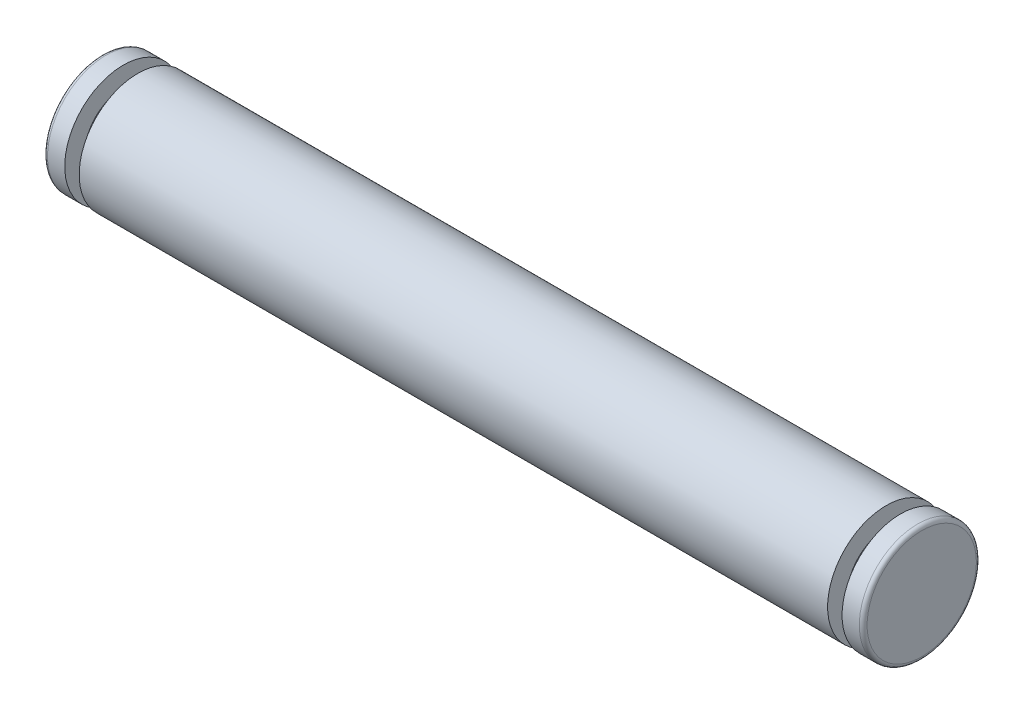
SolidWorks part; units mm, degrees
ref_plane "Front Plane" through (0, 0, 0) normal (0, 0, 1) x (1, 0, 0)
ref_plane "Top Plane" through (0, 0, 0) normal (0, 1, 0) x (1, 0, 0)
ref_plane "Right Plane" through (0, 0, 0) normal (1, 0, 0) x (0, 0, -1)
sketch "Sketch1" plane through (0, 0, 0) normal (0, 1, 0) x (1, 0, 0)
  line L0 (-21, 0) -> (0, 0) construction
  line L1 (0, 0) -> (21, 0) construction
  line L2 (0, 0) -> (0, 4.0847) construction
  line L3 (-19.177, 3) -> (19.177, 3)
  line L4 (19.177, 3) -> (19.177, 2)
  line L5 (19.177, 2) -> (19.917, 2)
  line L6 (19.917, 2) -> (19.917, 3)
  line L7 (19.917, 3) -> (20.8, 3)
  line L8 (21, 2.8) -> (21, 0)
  line L9 (-21, 2.8) -> (-21, 0)
  line L10 (-19.917, 3) -> (-20.8, 3)
  line L11 (-19.917, 2) -> (-19.917, 3)
  line L12 (-19.177, 2) -> (-19.917, 2)
  line L13 (-19.177, 3) -> (-19.177, 2)
  line L14 (21, 0) -> (-21, 0)
  arc A0 (20.8, 3) -> (21, 2.8) centre (20.8, 2.8) cw
  arc A1 (-21, 2.8) -> (-20.8, 3) centre (-20.8, 2.8) cw
  point P8 (0, 3)
  point P14 (21, 3)
  point P21 (-21, 3)
  dimension "D6" = 0.2
  dimension "D1" = 38.354
  dimension "D2" = 3
  dimension "D3" = 2
  dimension "D4" = 0.74
  dimension "D5" = 42
revolve "Revolve1" add sketch "Sketch1" angle 360 about L14
